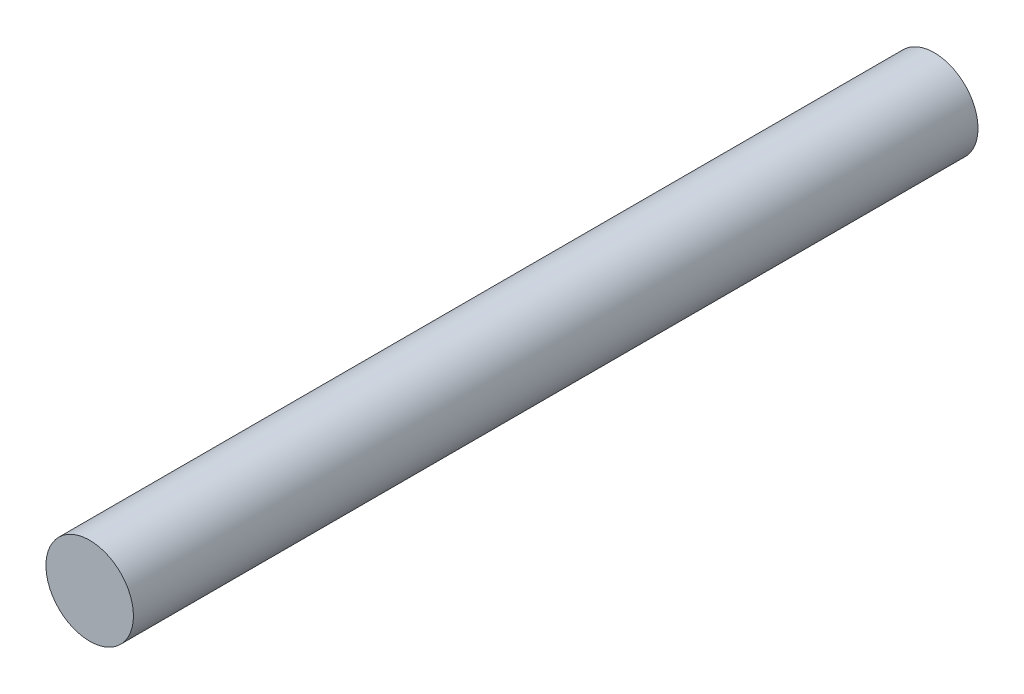
SolidWorks part; units mm, degrees
ref_plane "Front Plane" through (0, 0, 0) normal (0, 0, 1) x (1, 0, 0)
ref_plane "Top Plane" through (0, 0, 0) normal (0, 1, 0) x (1, 0, 0)
ref_plane "Right Plane" through (0, 0, 0) normal (1, 0, 0) x (0, 0, -1)
sketch "Sketch1" plane through (0, 0, 0) normal (0, 0, 1) x (1, 0, 0)
  circle A0 centre (0, 0) radius 2.5
  dimension "D1" = 5
extrude "Boss-Extrude1" add sketch "Sketch1" along normal blind 48.25
